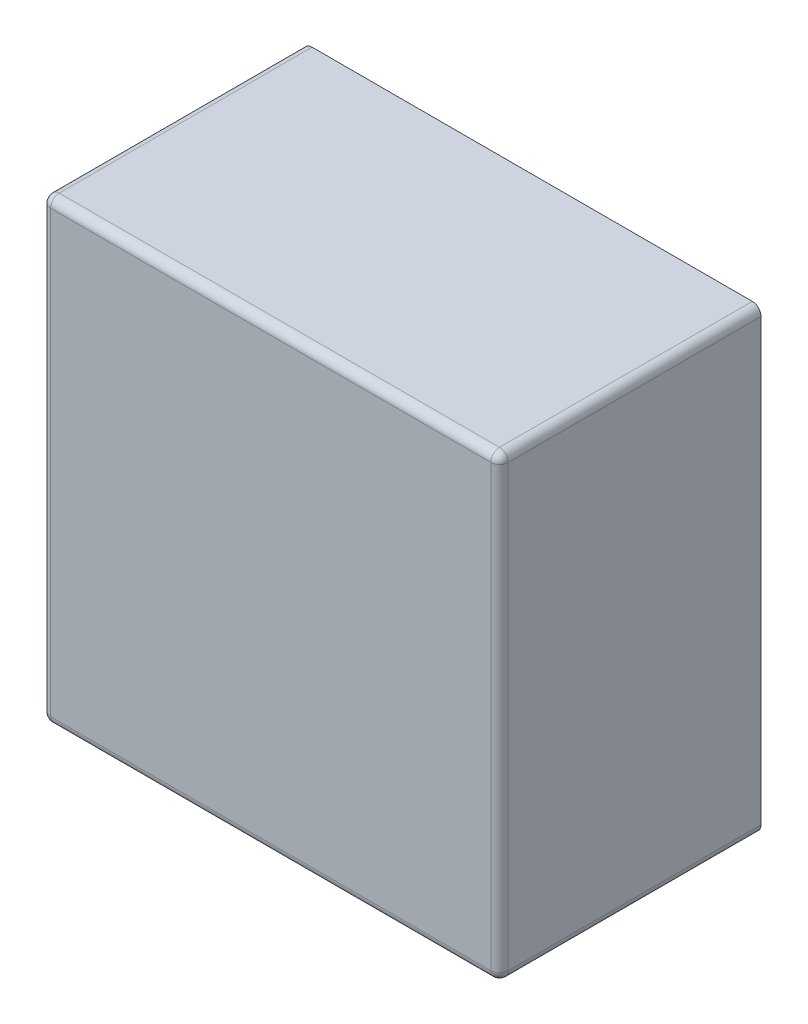
SolidWorks part; units mm, degrees
ref_plane "Alzado" through (0, 0, 0) normal (0, 0, 1) x (1, 0, 0)
ref_plane "Planta" through (0, 0, 0) normal (0, 1, 0) x (1, 0, 0)
ref_plane "Vista lateral" through (0, 0, 0) normal (1, 0, 0) x (0, 0, -1)
sketch "Croquis1" plane through (0, 0, 0) normal (0, 0, 1) x (1, 0, 0)
  line L1 (0, 0) -> (105, 0)
  line L2 (0, 0) -> (0, -105)
  line L3 (0, -105) -> (105, -105)
  line L4 (105, 0) -> (105, -105)
  dimension "D1" = 105
  dimension "D2" = 105
extrude "Saliente-Extruir1" add sketch "Croquis1" along normal blind 60
fillet "Redondeo1" radius 2 8 edges at (105, -105, 30) (52.5, -105, 60) (0, -105, 30) (105, -52.5, 60) (105, 0, 30) (0, -52.5, 60) (0, 0, 30) (52.5, 0, 60)
